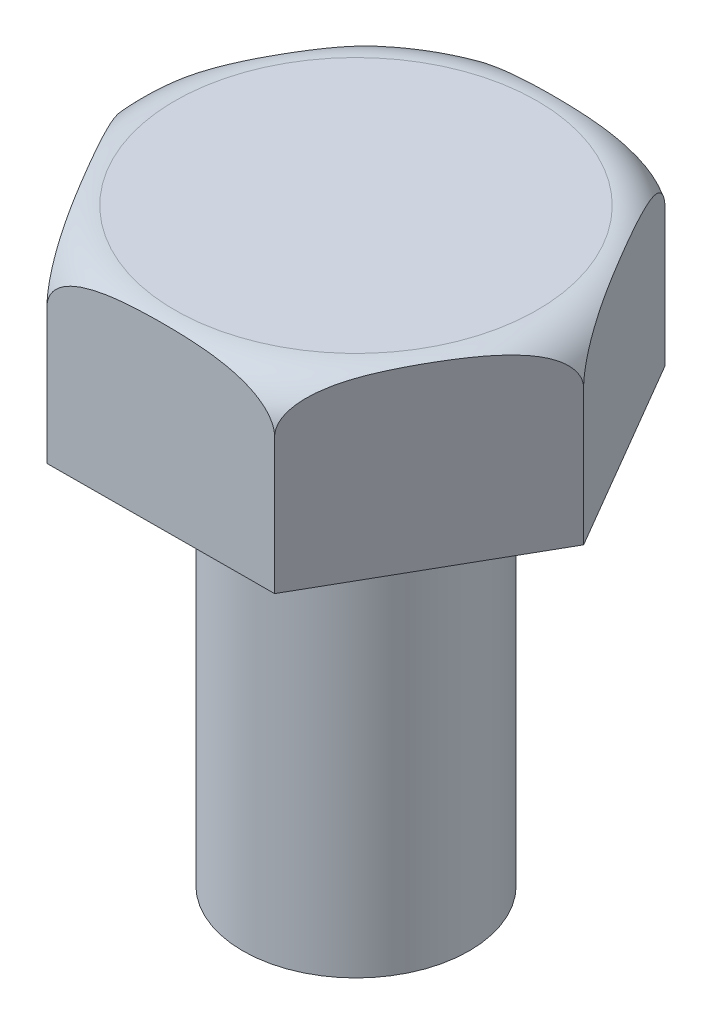
SolidWorks part; units mm, degrees
ref_plane "Front Plane" through (0, 0, 0) normal (0, 0, 1) x (1, 0, 0)
ref_plane "Top Plane" through (0, 0, 0) normal (0, 1, 0) x (1, 0, 0)
ref_plane "Right Plane" through (0, 0, 0) normal (1, 0, 0) x (0, 0, -1)
sketch "Sketch1" plane through (0, 0, 0) normal (0, 1, 0) x (1, 0, 0)
  circle A0 centre (0, 0) radius 5
extrude "Boss-Extrude1" add sketch "Sketch1" along normal mid plane 13
sketch "Sketch2" plane through (0, -6.5, 0) normal (0, -1, 0) x (1, 0, 0)
  circle A0 centre (0, 0) radius 2.5
  circle A1 centre (0, 0) radius 5
extrude "Cut-Extrude1" cut sketch "Sketch2" against normal blind 9
sketch "Sketch4" plane through (0, 6.5, 0) normal (0, 1, 0) x (1, 0, 0)
  line L1 (2.4785, 4.3424) -> (-2.5214, 4.3177)
  line L2 (-2.5214, 4.3177) -> (-4.9999, -0.0247)
  line L3 (-4.9999, -0.0247) -> (-2.4785, -4.3424)
  line L4 (-2.4785, -4.3424) -> (2.5214, -4.3177)
  line L5 (2.5214, -4.3177) -> (4.9999, 0.0247)
  line L6 (4.9999, 0.0247) -> (2.4785, 4.3424)
  circle A1 centre (0, 0) radius 5
  circle M1 centre (0, 0) radius 5
extrude "Cut-Extrude2" cut sketch "Sketch4" against normal blind 4 contours L2 M1 | L3 M1 | L4 M1 | L5 M1 | L6 M1 | L1 M1
sketch "Sketch5" plane through (0, 0, 0) normal (0, 0, 1) x (1, 0, 0)
  line L0 (-3.7223, 6.5) -> (-3.7223, 8.0605)
  line L1 (-4.9999, 6.5) -> (-2.4785, 6.5) construction
  line L2 (-3.7223, 8.0605) -> (-6.7407, 6.1073)
  line L3 (-6.7407, 6.1073) -> (-4.9999, 5.0595)
  line L4 (-4.9999, 2.5) -> (-4.9999, 6.5) construction
  line L5 (-4.9999, 5.0595) -> (-4.9999, 5.5)
  line L6 (-3.9999, 6.5) -> (-3.7223, 6.5)
  line L7 (0, 0) -> (0, 8.3301) construction
  arc A0 (-4.9999, 5.5) -> (-3.9999, 6.5) centre (-3.9999, 5.5) cw
  point P12 (-4.9999, 6.5)
  dimension "D1" = 1
revolve "Cut-Revolve1" cut sketch "Sketch5" angle 360 about L7
